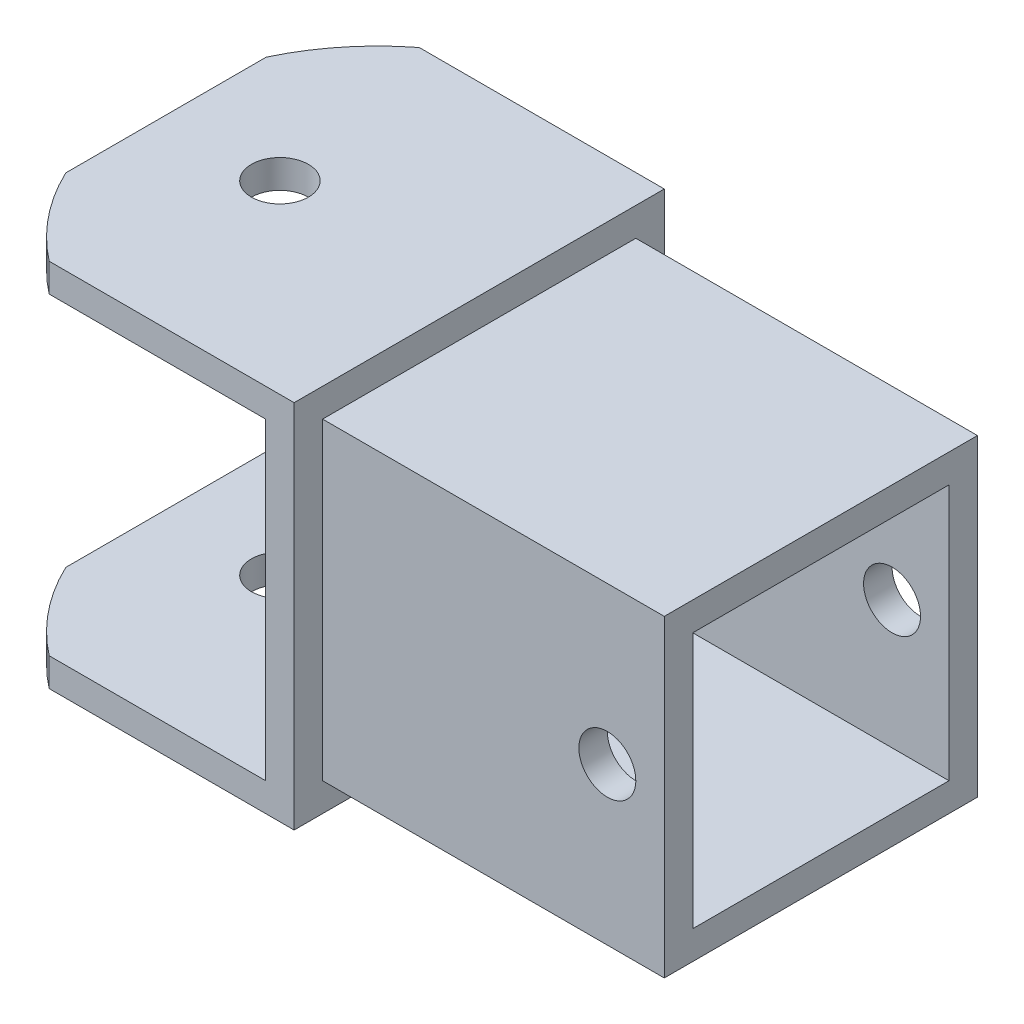
SolidWorks part; units mm, degrees
ref_plane "Front Plane" through (0, 0, 0) normal (0, 0, 1) x (1, 0, 0)
ref_plane "Top Plane" through (0, 0, 0) normal (0, 1, 0) x (1, 0, 0)
ref_plane "Right Plane" through (0, 0, 0) normal (1, 0, 0) x (0, 0, -1)
sketch "Sketch2" plane through (0, 0, 0) normal (0, 1, 0) x (1, 0, 0)
  line L0 (-50.8, 38.1) -> (76.2, 38.1)
  line L1 (76.2, 38.1) -> (76.2, -101.6)
  line L2 (76.2, -101.6) -> (-50.8, -101.6)
  line L3 (-50.8, -101.6) -> (-50.8, -114.3)
  line L4 (-50.8, -114.3) -> (88.9, -114.3)
  line L5 (88.9, -114.3) -> (88.9, 50.8)
  line L6 (88.9, 50.8) -> (-50.8, 50.8)
  line L7 (-50.8, 50.8) -> (-50.8, 38.1)
  point P2 (19.05, -114.3)
  point P9 (12.7, 38.1)
  dimension "D1" = 12.7
  dimension "D2" = 12.7
  dimension "D3" = 12.7
  dimension "D4" = 139.7
  dimension "D5" = 38.1
  dimension "D6" = 127
  dimension "D8" = 76.2
extrude "Boss-Extrude1" add sketch "Sketch2" along normal mid plane 165.1
sketch "Sketch4" plane through (88.9, 0, 0) normal (1, 0, 0) x (0, 0, -1)
  line L0 (50.8, 82.55) -> (50.8, -82.55) construction
  line L5 (-88.9, 57.15) -> (25.4, 57.15)
  line L6 (-88.9, 57.15) -> (-88.9, -57.15)
  line L11 (-88.9, -57.15) -> (25.4, -57.15)
  line L12 (25.4, 57.15) -> (25.4, -57.15)
  line L13 (-88.9, 57.15) -> (25.4, -57.15) construction
  line L14 (-88.9, -57.15) -> (25.4, 57.15) construction
  line L15 (-101.6, 69.85) -> (38.1, 69.85)
  line L16 (-101.6, 69.85) -> (-101.6, -69.85)
  line L17 (-101.6, -69.85) -> (38.1, -69.85)
  line L18 (38.1, 69.85) -> (38.1, -69.85)
  line L19 (-101.6, 69.85) -> (38.1, -69.85) construction
  line L20 (-101.6, -69.85) -> (38.1, 69.85) construction
  line L21 (-114.3, 82.55) -> (-114.3, -82.55) construction
  line L25 (-114.3, 82.55) -> (50.8, 82.55) construction
  point P0 (-31.75, 0)
  point P6 (-31.75, 0)
  dimension "D1" = 69.85
  dimension "D2" = 82.55
  dimension "D3" = 165.1
  dimension "D4" = 12.7
  dimension "D5" = 12.7
  dimension "D6" = 12.7
extrude "Boss-Extrude2" add sketch "Sketch4" along normal blind 152.4
sketch "Sketch5" plane through (0, 0, 114.3) normal (0, 0, 1) x (1, 0, 0)
  circle A0 centre (0, 0) radius 12.7
  dimension "D1" = 25.4
extrude "Cut-Extrude1" cut sketch "Sketch5" against normal through all both and the other way through all
sketch "Sketch6" plane through (0, 69.85, 0) normal (0, 1, 0) x (1, 0, 0)
  line L0 (241.3, 38.1) -> (241.3, -101.6) construction
  line L1 (241.3, 38.1) -> (88.9, 38.1) construction
  circle A0 centre (215.9, -31.75) radius 12.7
  dimension "D1" = 25.4
  dimension "D2" = 25.4
  dimension "D3" = 69.85
extrude "Cut-Extrude2" cut sketch "Sketch6" against normal through all both and the other way through all
sketch "Sketch7" plane through (0, 0, 114.3) normal (0, 0, 1) x (1, 0, 0)
  line L0 (-50.8, 82.55) -> (88.9, 82.55) construction
  line L1 (-50.8, -82.55) -> (88.9, -82.55) construction
  line L2 (-20.3743, 82.55) -> (-68.4291, 82.55)
  line L3 (-68.4291, 82.55) -> (-68.4291, -82.55)
  line L4 (-68.4291, -82.55) -> (-20.3743, -82.55)
  arc A0 (-20.3743, 82.55) -> (-20.3743, -82.55) centre (43.5565, 0) ccw
extrude "Cut-Extrude4" cut sketch "Sketch7" against normal through all both and the other way through all contours L3 L4 A0 L2
move or copy body "Body-Move/Copy1" bodies to move or copy 106 copy no rotation origin (0, 0, 31.7503) rotation axis (1, 0, 0) rotation angle 90
